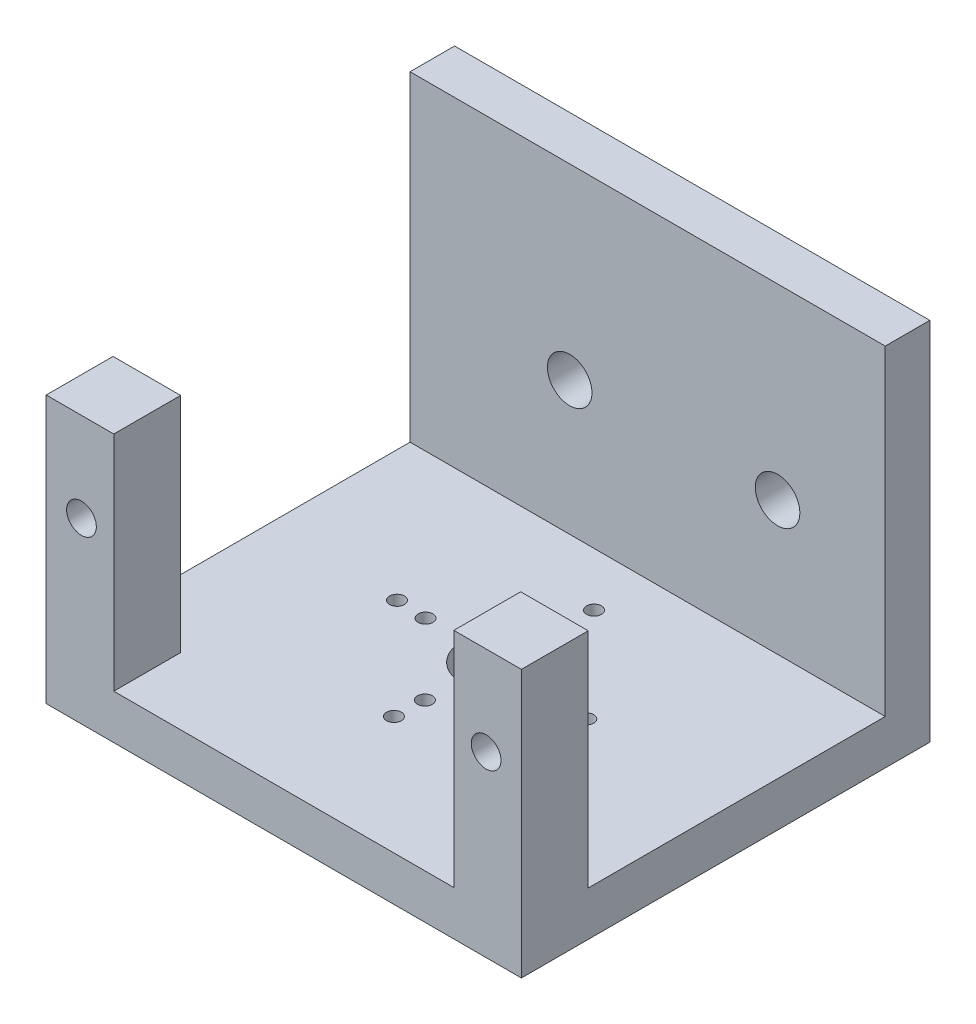
SolidWorks part; units mm, degrees
ref_plane "Front Plane" through (0, 0, 0) normal (0, 0, 1) x (1, 0, 0)
ref_plane "Top Plane" through (0, 0, 0) normal (0, 1, 0) x (1, 0, 0)
ref_plane "Right Plane" through (0, 0, 0) normal (1, 0, 0) x (0, 0, -1)
sketch "Sketch1" plane through (0, 0, 0) normal (0, 1, 0) x (1, 0, 0)
  line L1 (0, 0) -> (100, 0)
  line L2 (0, 0) -> (0, 100)
  line L3 (0, 100) -> (100, 100)
  line L4 (100, 0) -> (100, 100)
  dimension "D1" = 100
  dimension "D2" = 100
extrude "Boss-Extrude1" add sketch "Sketch1" along normal blind 3
sketch "Sketch2" plane through (0, 0, 0) normal (0, -1, 0) x (1, 0, 0)
  line L0 (0, -100) -> (0, 0) construction
  line L1 (100, -100) -> (0, -100)
  line L2 (100, -100) -> (100, -25.77)
  line L3 (66.659, -25.77) -> (22.9499, -25.77)
  line L4 (0, -100) -> (0, -25.77)
  line L5 (22.9499, -25.77) -> (22.9499, 0)
  line L6 (0, 0) -> (100, 0) construction
  line L7 (22.9499, 0) -> (0, 0)
  line L8 (0, 0) -> (0, -25.77)
  line L9 (100, -25.77) -> (100, 0)
  line L10 (100, 0) -> (66.659, 0)
  line L11 (66.659, 0) -> (66.659, -25.77)
extrude "Cut-Extrude1" cut sketch "Sketch2" against normal blind 10
sketch "Sketch3" plane through (0, 0, -25.77) normal (0, 0, -1) x (-1, 0, 0)
  line L1 (-66.659, 0) -> (-22.9499, 0)
  line L2 (-66.659, 0) -> (-66.659, 24.603)
  line L3 (-66.659, 24.603) -> (-22.9499, 24.603)
  line L4 (-22.9499, 0) -> (-22.9499, 24.603)
extrude "Boss-Extrude2" add sketch "Sketch3" against normal blind 3 contours L3 L4 L1 L2
sketch "Sketch4" plane through (0, 0, 0) normal (0, 0, 1) x (1, 0, 0)
  line L1 (66.659, 0) -> (22.9499, 0)
  line L2 (66.659, 0) -> (66.659, 3)
  line L3 (66.659, 3) -> (22.9499, 3)
  line L4 (22.9499, 0) -> (22.9499, 3)
extrude "Boss-Extrude3" add sketch "Sketch4" along normal up to surface (1.73 mm away)
sketch "Sketch6" plane through (0, 0, 1.73) normal (0, 0, 1) x (1, 0, 0)
  line L1 (66.659, 3) -> (62.109, 3)
  line L2 (66.659, 3) -> (66.659, 18)
  line L3 (66.659, 18) -> (62.109, 18)
  line L4 (62.109, 3) -> (62.109, 18)
  line L5 (39.209, 18) -> (34.659, 18)
  line L6 (39.209, 18) -> (39.209, 3)
  line L7 (39.209, 3) -> (34.659, 3)
  line L8 (34.659, 18) -> (34.659, 3)
extrude "Boss-Extrude4" add sketch "Sketch6" against normal up to surface (4.5 mm away)
sketch "Sketch7" plane through (22.9499, 0, 0) normal (-1, 0, 0) x (0, 0, 1)
  line L1 (-25.77, 24.603) -> (1.73, 24.603)
  line L2 (-25.77, 24.603) -> (-25.77, 0)
  line L3 (-25.77, 0) -> (1.73, 0)
  line L4 (1.73, 24.603) -> (1.73, 0)
extrude "Cut-Extrude2" cut sketch "Sketch7" against normal up to surface (11.7091 mm away) up to face at (34.659, 10.5, -0.52)
sketch "Sketch9" plane through (0, 0, -2.77) normal (0, 0, -1) x (-1, 0, 0)
  circle A0 centre (-37.034, 12) radius 1
  arc A1 (-36.168, 12.5) -> (-36.168, 11.5) centre (-37.034, 12) ccw construction
  circle A2 centre (-64.284, 12) radius 1
  arc A3 (-65.15, 11.5) -> (-65.15, 12.5) centre (-64.284, 12) ccw construction
extrude "Cut-Extrude3" cut sketch "Sketch9" against normal blind 10
sketch "Sketch10" plane through (0, 0, 0) normal (0, -1, 0) x (1, 0, 0)
  circle A0 centre (50.1173, -6.2306) radius 0.5
  circle A1 centre (50.1994, -8.2289) radius 0.5
  circle A2 centre (54.7345, -12.6465) radius 0.5
  circle A3 centre (45.4423, -13.0282) radius 0.5
  circle A4 centre (50.5666, -17.1714) radius 0.5
  circle A5 centre (50.6487, -19.1697) radius 0.5
  circle A6 centre (56.7328, -12.5645) radius 0.5
  circle A7 centre (43.444, -13.1103) radius 0.5
extrude "Cut-Extrude4" cut sketch "Sketch10" against normal blind 10
sketch "Sketch11" plane through (0, 0, -25.77) normal (0, 0, -1) x (-1, 0, 0)
  circle A0 centre (-45.409, 12) radius 1.5
  circle A3 centre (-45.409, 12) radius 2.3 construction
  point P3 (0, 0)
  dimension "D1" = 3
sketch "Sketch12" plane through (0, 0, 0) normal (0, -1, 0) x (1, 0, 0)
  circle A0 centre (50.3881, -12.8251) radius 2.35
  circle A1 centre (50.3881, -12.8251) radius 2.35 construction
extrude "Cut-Extrude6" cut sketch "Sketch12" against normal blind 10
extrude "Cut-Extrude7" cut sketch "Sketch11" against normal blind 10
sketch "Sketch13" plane through (0, 0, -25.77) normal (0, 0, -1) x (-1, 0, 0)
  circle A0 centre (-59.409, 12) radius 1.5
  circle A2 centre (-45.409, 12) radius 1.5 construction
  point P2 (0, 0)
  point P5 (-59.6811, 12)
  dimension "D1" = 3
  dimension "D2" = 14
extrude "Cut-Extrude8" cut sketch "Sketch13" against normal blind 10
